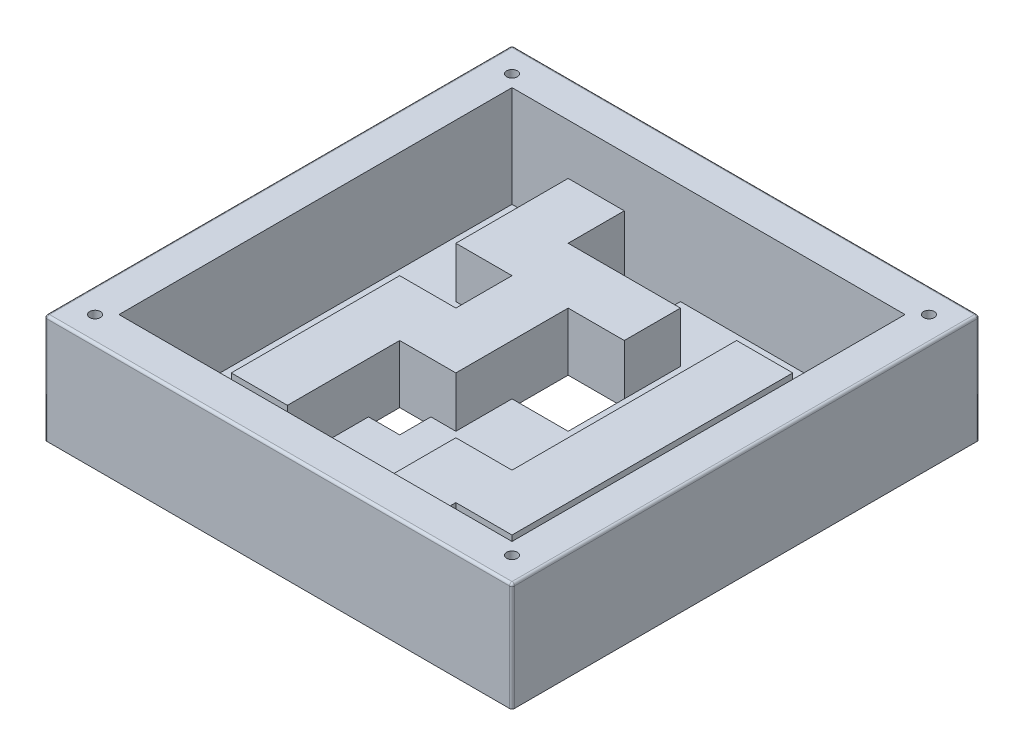
SolidWorks part; units mm, degrees
ref_plane "Plan de face" through (0, 0, 0) normal (0, 0, 1) x (1, 0, 0)
ref_plane "Plan de dessus" through (0, 0, 0) normal (0, 1, 0) x (1, 0, 0)
ref_plane "Plan de droite" through (0, 0, 0) normal (1, 0, 0) x (0, 0, -1)
sketch "Esquisse2" plane through (0, 0, 0) normal (0, 1, 0) x (1, 0, 0)
  line L1 (-92.5, 92.5) -> (92.5, 92.5)
  line L2 (-92.5, 92.5) -> (-92.5, -92.5)
  line L3 (-92.5, -92.5) -> (92.5, -92.5)
  line L4 (92.5, 92.5) -> (92.5, -92.5)
  dimension "D1" = 185
  dimension "D2" = 185
  dimension "D3" = 92.5
  dimension "D4" = 92.5
extrude "Boss.-Extru.1" add sketch "Esquisse2" against normal blind 3
sketch "Esquisse3" plane through (0, 0, 0) normal (0, 1, 0) x (1, 0, 0)
  line L0 (-77.77, 77.77) -> (77.77, 77.77)
  line L1 (-92.5, 92.5) -> (92.5, 92.5)
  line L2 (-92.5, 92.5) -> (-92.5, -92.5)
  line L3 (-92.5, -92.5) -> (92.5, -92.5)
  line L4 (92.5, 92.5) -> (92.5, -92.5)
  line L8 (77.77, 77.77) -> (77.77, -77.77)
  line L9 (-77.77, -77.77) -> (77.77, -77.77)
  line L10 (-77.77, 77.77) -> (-77.77, -77.77)
  dimension "D2" = 155.54
  dimension "D3" = 155.54
  dimension "D1" = 14.73
extrude "Boss.-Extru.2" add sketch "Esquisse3" along normal blind 40
sketch "Esquisse4" plane through (0, 0, 0) normal (0, 1, 0) x (1, 0, 0)
  line L0 (-55.55, 77.77) -> (-33.33, 77.77)
  line L1 (77.77, 77.77) -> (-77.77, 77.77) construction
  line L2 (-33.33, 77.77) -> (-33.33, 55.55)
  line L3 (-33.33, 55.55) -> (11.11, 55.55)
  line L4 (11.11, 55.55) -> (11.11, 33.33)
  line L5 (11.11, 33.33) -> (-11.11, 33.33)
  line L6 (-11.11, 33.33) -> (-11.11, -11.11)
  line L8 (-33.33, -11.11) -> (-33.33, -55.55)
  line L9 (-33.33, -55.55) -> (-55.55, -55.55)
  line L13 (-33.33, -11.11) -> (-11.11, -11.11)
  line L14 (-55.55, 77.77) -> (-55.55, 33.33)
  line L15 (-55.55, 33.33) -> (-33.33, 33.33)
  line L16 (-33.33, 33.33) -> (-33.33, 11.11)
  line L17 (-33.33, 11.11) -> (-55.55, 11.11)
  line L18 (-55.55, 11.11) -> (-55.55, -55.55)
  line L19 (-77.77, 77.77) -> (-77.77, -77.77) construction
  line L20 (-77.77, -77.77) -> (77.77, -77.77) construction
  line L21 (77.77, -77.77) -> (77.77, 77.77) construction
  line L22 (33.33, 55.55) -> (55.55, 55.55)
  line L23 (33.33, 55.55) -> (33.33, -33.33)
  line L25 (55.55, 55.55) -> (55.55, -55.55)
  line L28 (55.55, -55.55) -> (33.33, -55.55)
  line L30 (33.33, -33.33) -> (11.11, -33.33)
  line L32 (33.33, -77.77) -> (11.11, -77.77)
  line L33 (11.11, -33.33) -> (11.11, -77.77)
  line L34 (33.33, -55.55) -> (33.33, -77.77)
  line L35 (77.77, -77.77) -> (77.77, 77.77) construction
  dimension "D1" = 22.22
  dimension "D2" = 22.22
  dimension "D3" = 22.22
  dimension "D4" = 22.22
  dimension "D5" = 22.22
  dimension "D6" = 22.22
  dimension "D7" = 22.22
  dimension "D8" = 22.22
  dimension "D9" = 22.22
  dimension "D10" = 66.66
  dimension "D11" = 22.22
  dimension "D12" = 22.22
  dimension "D13" = 22.22
  dimension "D14" = 22.22
  dimension "D15" = 22.22
  dimension "D16" = 22.22
  dimension "D17" = 22.22
  dimension "D18" = 44.44
extrude "Boss.-Extru.3" add sketch "Esquisse4" along normal blind 20
sketch "Esquisse5" plane through (0, 0, 0) normal (0, 1, 0) x (1, 0, 0)
  line L0 (77.77, 77.77) -> (-33.33, 77.77) construction
  line L1 (-33.33, 55.55) -> (-11.11, 55.55)
  line L2 (-33.33, 55.55) -> (-33.33, 77.77)
  line L3 (-33.33, 77.77) -> (-11.11, 77.77)
  line L4 (-11.11, 55.55) -> (-11.11, 77.77)
  line L5 (-11.11, -11.11) -> (-11.11, 33.33) construction
  line L6 (-11.11, 33.33) -> (11.11, 33.33)
  line L7 (-11.11, 33.33) -> (-11.11, 11.11)
  line L8 (-11.11, 11.11) -> (11.11, 11.11)
  line L9 (11.11, 33.33) -> (11.11, 11.11)
  line L10 (11.11, 33.33) -> (11.11, 55.55) construction
  line L11 (-33.33, 11.11) -> (-55.55, 11.11) construction
  line L12 (33.33, -55.55) -> (55.55, -55.55) construction
  line L13 (-33.33, -11.11) -> (-20.98, -11.11)
  line L14 (-33.33, -11.11) -> (-33.33, -23.46)
  line L15 (-33.33, -23.46) -> (-20.98, -23.46)
  line L16 (-20.98, -11.11) -> (-20.98, -23.46)
  line L17 (-72.835, 28.395) -> (-60.485, 28.395)
  line L18 (-72.835, 28.395) -> (-72.835, 16.045)
  line L19 (-72.835, 16.045) -> (-60.485, 16.045)
  line L20 (-60.485, 28.395) -> (-60.485, 16.045)
  line L21 (-72.835, -60.485) -> (-60.485, -60.485)
  line L22 (-72.835, -60.485) -> (-72.835, -72.835)
  line L23 (-72.835, -72.835) -> (-60.485, -72.835)
  line L24 (-60.485, -60.485) -> (-60.485, -72.835)
  line L25 (60.485, -60.485) -> (72.835, -60.485)
  line L26 (60.485, -60.485) -> (60.485, -72.835)
  line L27 (60.485, -72.835) -> (72.835, -72.835)
  line L28 (72.835, -60.485) -> (72.835, -72.835)
  line L29 (11.11, -55.55) -> (-1.24, -55.55)
  line L30 (11.11, -55.55) -> (11.11, -43.2)
  line L31 (11.11, -43.2) -> (-1.24, -43.2)
  line L32 (-1.24, -55.55) -> (-1.24, -43.2)
  line L34 (11.11, -33.33) -> (11.11, -77.77) construction
  line L35 (-77.77, 77.77) -> (-77.77, -77.77) construction
  line L36 (-55.55, 33.33) -> (-33.33, 33.33) construction
  line L37 (-55.55, 77.77) -> (-55.55, 33.33) construction
  line L38 (-77.77, -77.77) -> (11.11, -77.77) construction
  line L39 (77.77, -77.77) -> (77.77, 77.77) construction
  dimension "D1" = 12.35
  dimension "D2" = 12.35
  dimension "D3" = 12.35
  dimension "D4" = 12.35
  dimension "D5" = 12.35
  dimension "D6" = 12.35
  dimension "D7" = 12.35
  dimension "D8" = 12.35
  dimension "D9" = 12.35
  dimension "D10" = 12.35
  dimension "D11" = 4.935
  dimension "D12" = 4.935
  dimension "D13" = 4.935
  dimension "D14" = 4.935
  dimension "D15" = 4.935
  dimension "D16" = 4.935
extrude "Enlèv. mat.-Extru.1" cut sketch "Esquisse5" against normal up to next
fillet "Congé1" radius 1 8 edges at (-92.5, 18.5, -92.5) (-92.5, 18.5, 92.5) (-92.5, 40, 0) (0, 40, 92.5) (0, 40, -92.5) (92.5, 40, 0) (92.5, 18.5, -92.5) (92.5, 18.5, 92.5)
sketch "Esquisse6" plane through (0, 40, 0) normal (0, 1, 0) x (1, 0, 0)
  line L0 (92.5, 91.5) -> (92.5, -91.5) construction
  line L1 (-91.5, 92.5) -> (91.5, 92.5) construction
  line L2 (91.5, -92.5) -> (-91.5, -92.5) construction
  line L3 (-92.5, -91.5) -> (-92.5, 91.5) construction
  circle A0 centre (-82.5, -82.5) radius 1.1
  circle A1 centre (82.5, -82.5) radius 1.1
  circle A2 centre (82.5, 82.5) radius 1.1
  circle A3 centre (-82.5, 82.5) radius 1.1
  dimension "D1" = 2.2
  dimension "D2" = 10
  dimension "D3" = 10
  dimension "D4" = 10
  dimension "D5" = 10
extrude "Enlèv. mat.-Extru.2" cut sketch "Esquisse6" against normal through all
sketch "Esquisse7" plane through (0, 40, 0) normal (0, 1, 0) x (1, 0, 0)
  circle A0 centre (-82.5, -82.5) radius 2.1
  circle A1 centre (-82.5, 82.5) radius 2.1
  circle A2 centre (82.5, 82.5) radius 2.1
  circle A3 centre (82.5, -82.5) radius 2.1
  dimension "D1" = 4.2
extrude "Enlèv. mat.-Extru.3" cut sketch "Esquisse7" against normal blind 41
